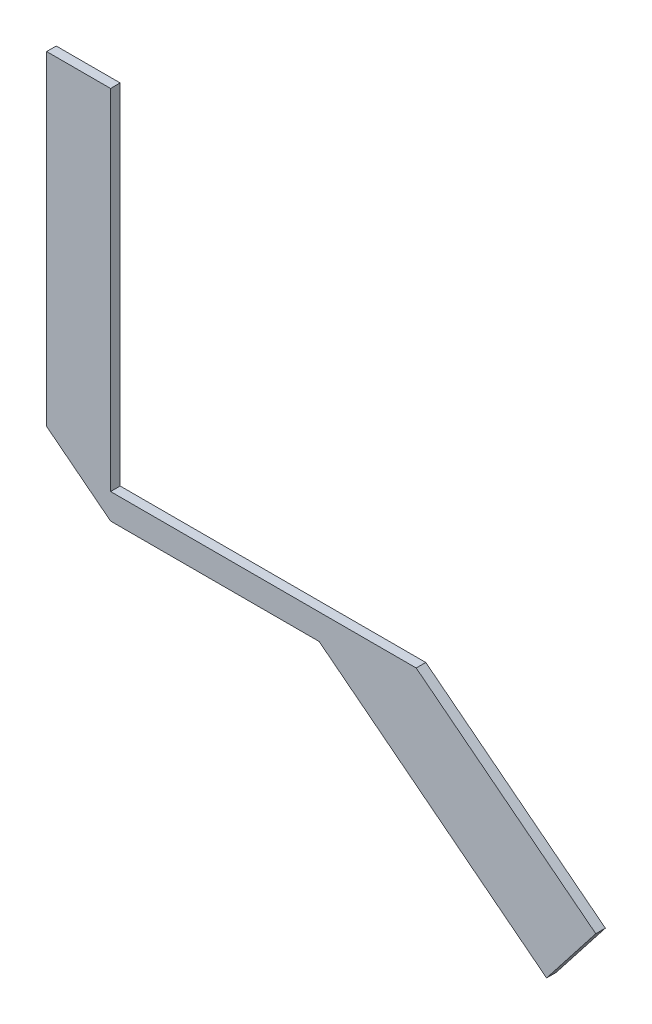
SolidWorks part; units mm, degrees
ref_plane "Front Plane" through (0, 0, 0) normal (0, 0, 1) x (1, 0, 0)
ref_plane "Top Plane" through (0, 0, 0) normal (0, 1, 0) x (1, 0, 0)
ref_plane "Right Plane" through (0, 0, 0) normal (1, 0, 0) x (0, 0, -1)
sketch "Sketch3" plane through (0, 0, -2) normal (0, 0, 1) x (1, 0, 0)
  line L0 (-331.8267, 452.4789) -> (-275.6472, 408.5867)
  line L1 (-447.4324, 585.7679) -> (-447.4324, 511.0745) construction
  line L2 (-275.6472, 408.5867) -> (-291.0387, 388.8864)
  line L3 (-291.0387, 388.8864) -> (-362.1939, 444.4789)
  line L4 (-335.6665, 455.4789) -> (-330.7937, 455.4789) construction
  line L5 (-275.6472, 408.5867) -> (-237.9324, 408.5867) construction
  line L6 (-331.8267, 452.4789) -> (-427.4324, 452.4789)
  line L7 (-237.9324, 312.3679) -> (-237.9324, 653.2679) construction
  line L10 (-427.4324, 561.68) -> (-447.4324, 561.68)
  line L11 (-427.4324, 452.4789) -> (-427.4324, 561.68)
  line L13 (-447.4324, 561.68) -> (-447.4324, 460.1046)
  line L15 (-362.1939, 444.4789) -> (-427.4324, 444.4789)
  line L16 (-427.4324, 444.4789) -> (-447.4324, 460.1046)
  line L18 (-277.0125, 409.6533) -> (-335.6665, 455.4789) construction
  line L19 (-447.4324, 511.0745) -> (-263.335, 367.2419) construction
  dimension "D1" = 8
  dimension "D2" = 3
  dimension "D3" = 20
extrude "Boss-Extrude1" add sketch "Sketch3" against normal blind 3
